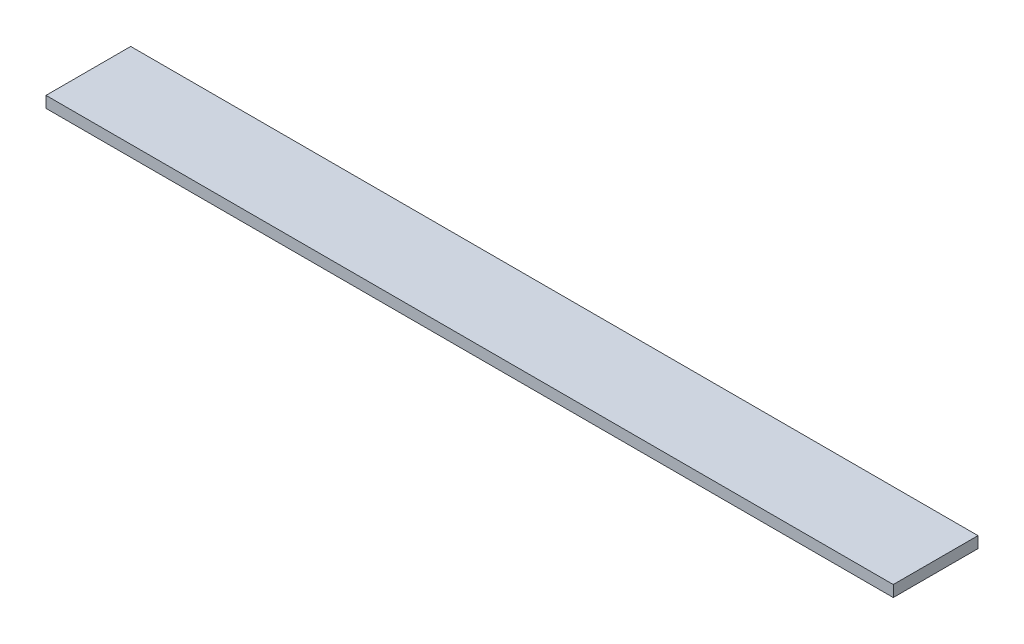
SolidWorks part; units mm, degrees
ref_plane "Спереди" through (0, 0, 0) normal (0, 0, 1) x (1, 0, 0)
ref_plane "Сверху" through (0, 0, 0) normal (0, 1, 0) x (1, 0, 0)
ref_plane "Справа" through (0, 0, 0) normal (1, 0, 0) x (0, 0, -1)
sketch "Эскиз1" plane through (0, 0, 0) normal (1, 0, 0) x (0, 0, -1)
  line L1 (-15, -2) -> (15, -2)
  line L2 (-15, -2) -> (-15, 2)
  line L3 (-15, 2) -> (15, 2)
  line L4 (15, -2) -> (15, 2)
  line L5 (-15, -2) -> (15, 2) construction
  line L6 (-15, 2) -> (15, -2) construction
  point P0 (0, 0)
  dimension "D1" = 4
  dimension "D2" = 30
extrude "Бобышка-Вытянуть1" add sketch "Эскиз1" along normal blind 300
